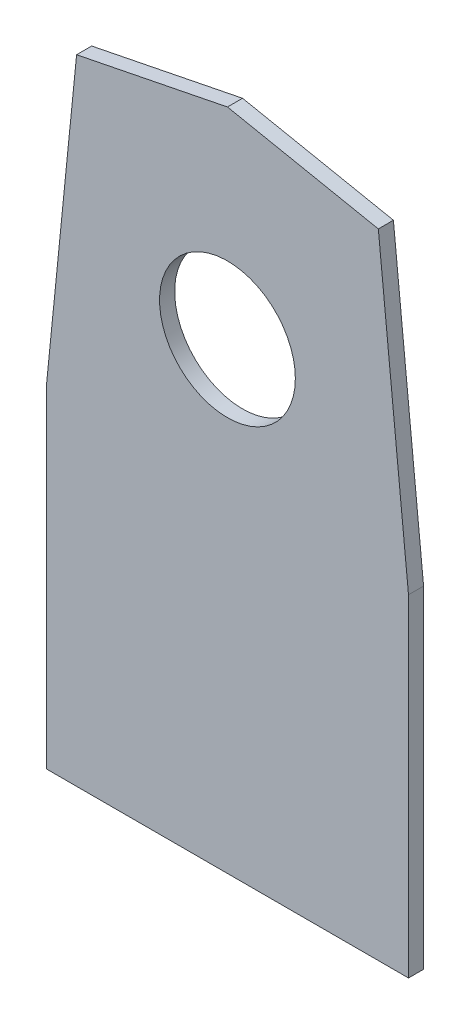
SolidWorks part; units mm, degrees
ref_plane "Front Plane" through (0, 0, 0) normal (0, 0, 1) x (1, 0, 0)
ref_plane "Top Plane" through (0, 0, 0) normal (0, 1, 0) x (1, 0, 0)
ref_plane "Right Plane" through (0, 0, 0) normal (1, 0, 0) x (0, 0, -1)
sketch "Sketch1" plane through (0, 0, 0) normal (0, 0, 1) x (1, 0, 0)
  line L0 (36.1801, 19.697) -> (29.8301, 83.197)
  line L1 (-40.0199, 89.547) -> (36.1801, 89.547)
  line L2 (-40.0199, 89.547) -> (-40.0199, -50.153)
  line L3 (-40.0199, -50.153) -> (36.1801, -50.153)
  line L4 (36.1801, 89.547) -> (36.1801, -50.153)
  line L5 (29.8301, 83.197) -> (-1.9199, 89.547)
  line L6 (-1.9199, 89.547) -> (-33.6699, 83.197)
  line L7 (-33.6699, 83.197) -> (-40.0199, 19.697)
  point P6 (0, 0)
  point P10 (0, 0)
  point P11 (0, 0)
  point P12 (0, 0)
  dimension "D1" = 76.2
  dimension "D2" = 139.7
  dimension "D3" = 69.85
  dimension "D4" = 69.85
  dimension "D5" = 63.5
  dimension "D6" = 63.5
  dimension "D7" = 63.5
  dimension "D8" = 6.35
extrude "Boss-Extrude1" add sketch "Sketch1" along normal blind 3.175 contours L6 L7 L2 L3 L4 L0 L5
sketch "Sketch2" plane through (0, 0, 3.175) normal (0, 0, 1) x (1, 0, 0)
  line L0 (-1.9199, 89.547) -> (-1.9199, 47.2052)
  circle A0 centre (-1.9199, 47.2052) radius 14.2875
  dimension "D2" = 28.575
  dimension "D1" = 42.3418
extrude "Cut-Extrude1" cut sketch "Sketch2" against normal blind 3.175
